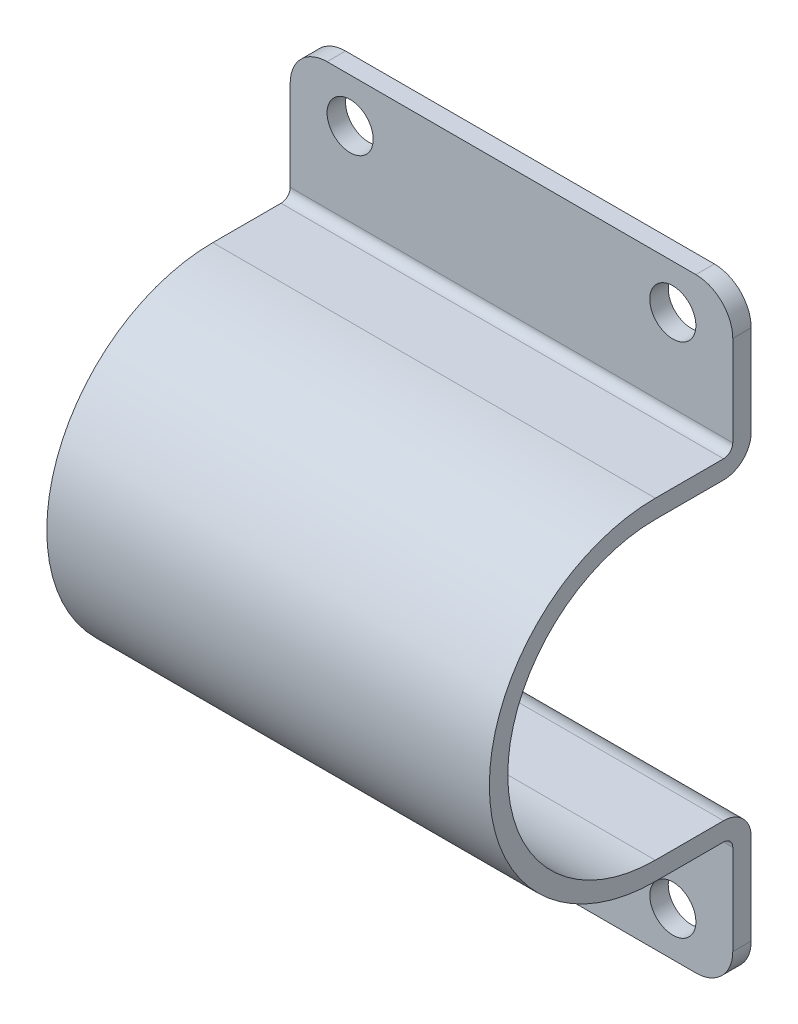
SolidWorks part; units mm, degrees
material "ABS"
ref_plane "Front Plane" through (0, 0, 0) normal (1, 0, 0) x (0, 1, 0)
ref_plane "Top Plane" through (0, 0, 0) normal (0, 0, 1) x (0, 1, 0)
ref_plane "Right Plane" through (0, 0, 0) normal (0, 1, 0) x (-1, 0, 0)
sketch "Sketch1" plane through (0, 0, 0) normal (1, 0, 0) x (0, 1, 0)
  line L0 (164, 0) -> (95, 0)
  line L1 (80, 15) -> (80, 52)
  line L2 (-80, 52) -> (-80, 15)
  line L3 (-95, 0) -> (-164, 0)
  line L4 (-164, 0) -> (-164, 10)
  line L5 (-164, 10) -> (-95, 10)
  line L6 (-90, 15) -> (-90, 52)
  line L7 (90, 52) -> (90, 15)
  line L8 (95, 10) -> (164, 10)
  line L9 (164, 10) -> (164, 0)
  arc A0 (80, 52) -> (-80, 52) centre (0, 52) ccw
  arc A1 (-90, 52) -> (90, 52) centre (0, 52) cw
  arc A2 (-95, 10) -> (-90, 15) centre (-95, 15) ccw
  arc A3 (90, 15) -> (95, 10) centre (95, 15) ccw
  arc A4 (95, 0) -> (80, 15) centre (95, 15) cw
  arc A5 (-80, 15) -> (-95, 0) centre (-95, 15) cw
  dimension "D1" = 10
  dimension "D6" = 80
  dimension "D3" = 90
  dimension "D7" = 5
  dimension "D8" = 15
  dimension "D2" = 52
  dimension "D4" = 328
  dimension "D5" = 164
extrude "Boss-Extrude1" add sketch "Sketch1" along normal blind 240
sketch "Sketch2" plane through (0, 0, 10) normal (0, 0, 1) x (1, 0, 0)
  line L8 (78.1, 0) -> (-78.1, 0) construction
  circle A0 centre (32.5, 140) radius 12.5
  circle A1 centre (207.5, 140) radius 12.5
  circle A2 centre (207.5, -140) radius 12.5
  circle A3 centre (32.5, -140) radius 12.5
  point P21 (0, 0)
  point P23 (0, 0)
  dimension "D4" = 25
  dimension "D5" = 25
  dimension "D1" = 140
  dimension "D2" = 175
extrude "Cut-Extrude1" cut sketch "Sketch2" against normal through all both and the other way through all
fillet "Fillet1" radius 20 4 edges at (0, -164, 5) (240, -164, 5) (0, 164, 5) (240, 164, 5)
